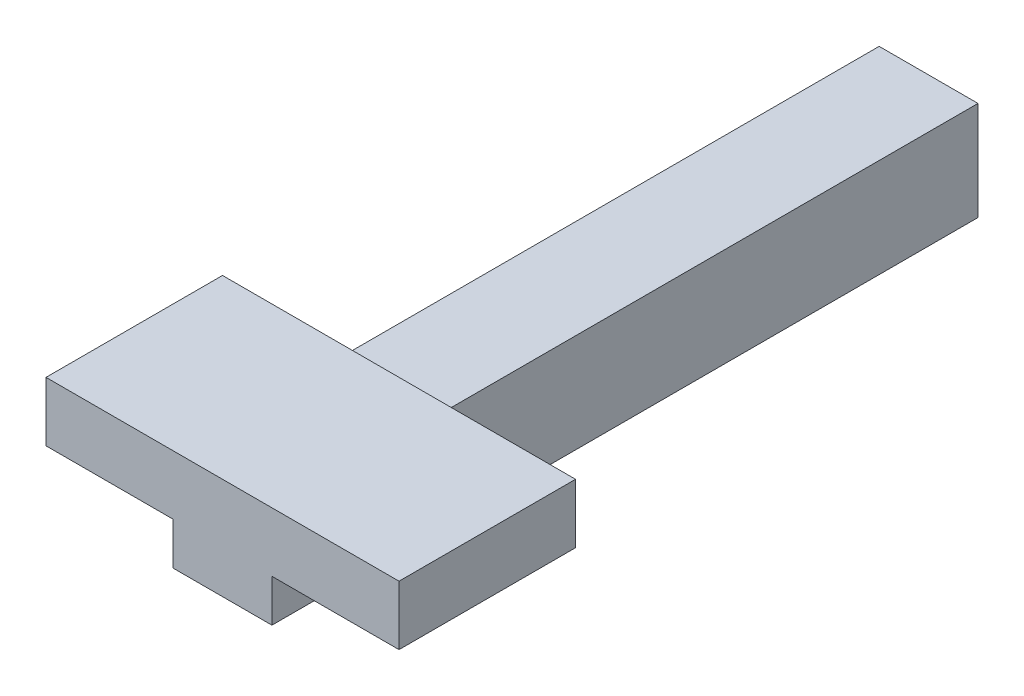
SolidWorks part; units mm, degrees
ref_plane "Front Plane" through (0, 0, 0) normal (0, 0, 1) x (1, 0, 0)
ref_plane "Top Plane" through (0, 0, 0) normal (0, 1, 0) x (1, 0, 0)
ref_plane "Right Plane" through (0, 0, 0) normal (1, 0, 0) x (0, 0, -1)
sketch "Sketch1" plane through (0, 0, 0) normal (0, 0, 1) x (1, 0, 0)
  line L1 (35, 35) -> (-35, 35)
  line L2 (35, 35) -> (35, -35)
  line L3 (35, -35) -> (-35, -35)
  line L4 (-35, 35) -> (-35, -35)
  line L5 (35, 35) -> (-35, -35) construction
  line L6 (35, -35) -> (-35, 35) construction
  point P0 (0, 0)
  dimension "D1" = 70
extrude "Boss-Extrude1" add sketch "Sketch1" along normal blind 500
sketch "Sketch2" plane through (0, 35, 0) normal (0, 1, 0) x (1, 0, 0)
  line L0 (35, -500) -> (-35, -500) construction
  line L1 (-125, -500) -> (125, -500)
  line L2 (-125, -500) -> (-125, -375)
  line L3 (-125, -375) -> (125, -375)
  line L4 (125, -500) -> (125, -375)
  line L5 (-125, -500) -> (125, -375) construction
  line L6 (-125, -375) -> (125, -500) construction
  point P0 (0, -437.5)
  point P5 (0, 0)
  dimension "D1" = 250
  dimension "D2" = 125
extrude "Boss-Extrude2" add sketch "Sketch2" against normal blind 40 and the other way blind 2
